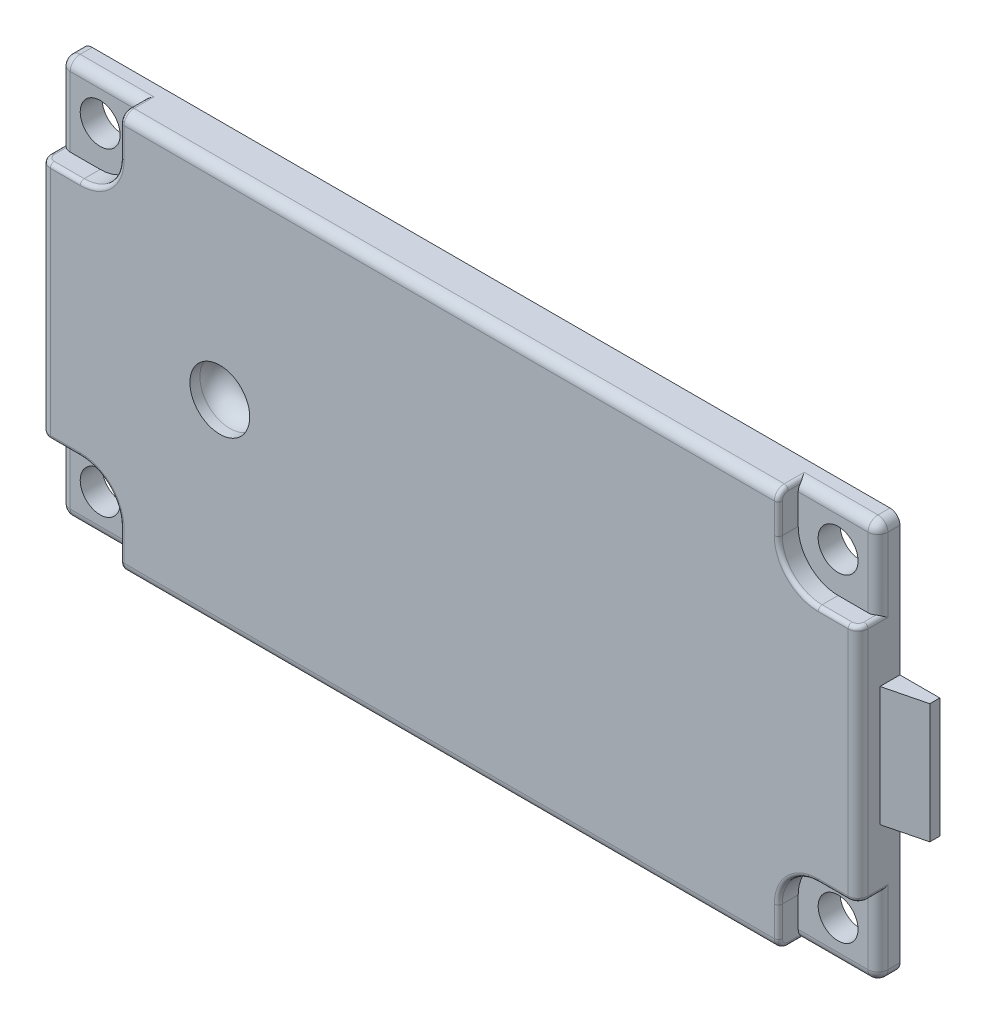
SolidWorks part; units mm, degrees
ref_plane "Front Plane" through (0, 0, 0) normal (0, 0, 1) x (1, 0, 0)
ref_plane "Top Plane" through (0, 0, 0) normal (0, 1, 0) x (1, 0, 0)
ref_plane "Right Plane" through (0, 0, 0) normal (1, 0, 0) x (0, 0, -1)
sketch "Sketch1" plane through (0, 0, 0) normal (0, 0, 1) x (1, 0, 0)
  line L0 (-20.5, -10) -> (20.5, 10) construction
  line L1 (-20.5, 10) -> (20.5, 10)
  line L2 (-20.5, 10) -> (-20.5, -10)
  line L3 (-20.5, -10) -> (20.5, -10)
  line L4 (20.5, 10) -> (20.5, -10)
  line L5 (-13.6353, 0) -> (-19.2524, 0) construction
  line L6 (0, 4.4253) -> (0, 7.9981) construction
  circle A0 centre (-18.5, 7.9981) radius 1
  circle A1 centre (-18.5, -7.9981) radius 1
  circle A2 centre (18.5, 7.9981) radius 1
  circle A3 centre (18.5, -7.9981) radius 1
  point P4 (0, 0)
  dimension "D3" = 2
  dimension "D1" = 20
  dimension "D2" = 41
  dimension "D4" = 2.0019
  dimension "D5" = 2
extrude "Extrude1" add sketch "Sketch1" along normal blind 2.1
sketch "Sketch2" plane through (0, 0, 2.1) normal (0, 0, 1) x (1, 0, 0)
  line L0 (0, 0) -> (31.1572, 0) construction
  line L1 (20.5, 10) -> (16.5, 10)
  line L2 (20.5, 10) -> (20.5, 6)
  line L3 (20.5, 6) -> (18.5, 6)
  line L4 (16.5, 10) -> (16.5, 8)
  line L5 (0, 0) -> (0, 18.9663) construction
  line L6 (16.5, -10) -> (16.5, -8)
  line L7 (20.5, -6) -> (18.5, -6)
  line L8 (20.5, -10) -> (20.5, -6)
  line L9 (20.5, -10) -> (16.5, -10)
  line L10 (-20.5, -10) -> (-16.5, -10)
  line L11 (-20.5, -10) -> (-20.5, -6)
  line L12 (-20.5, -6) -> (-18.5, -6)
  line L13 (-16.5, -10) -> (-16.5, -8)
  line L14 (-16.5, 10) -> (-16.5, 8)
  line L15 (-20.5, 6) -> (-18.5, 6)
  line L16 (-20.5, 10) -> (-20.5, 6)
  line L17 (-20.5, 10) -> (-16.5, 10)
  arc A0 (16.5, 8) -> (18.5, 6) centre (18.5, 8) ccw
  arc A3 (16.5, -8) -> (18.5, -6) centre (18.5, -8) cw
  arc A4 (-16.5, -8) -> (-18.5, -6) centre (-18.5, -8) ccw
  arc A7 (-16.5, 8) -> (-18.5, 6) centre (-18.5, 8) cw
  dimension "D3" = 2
  dimension "D1" = 4
  dimension "D2" = 4
extrude "Cut-Extrude1" cut sketch "Sketch2" against normal blind 1
fillet "Fillet1" radius 0.5 16 edges at (20.5, 0, 2.1) (-20.5, 0, 2.1) (0, -10, 2.1) (0, 10, 2.1) (-18.5, -10, 1.1) (-20.5, -8, 1.1) (-18.5, 10, 1.1) (-20.5, 8, 1.1) (18.5, 10, 1.1) (20.5, 8, 1.1) (20.5, -8, 1.1) (18.5, -10, 1.1) (-20.5, 10, 0.55) (-20.5, -10, 0.55) (20.5, 10, 0.55) (20.5, -10, 0.55)
fillet "Fillet2" radius 0.2 28 edges at (20.3536, -6, 1.9536) (19.25, -6, 2.1) (16.5, -9.8536, 1.9536) (16.5, -8.75, 2.1) (-16.5, -9.8536, 1.9536) (-16.5, -8.75, 2.1) (-20.3536, -6, 1.9536) (-19.25, -6, 2.1) (-20.3536, 6, 1.9536) (-19.25, 6, 2.1) (-16.5, 9.8536, 1.9536) (-16.5, 8.75, 2.1) (16.5, 9.8536, 1.9536) (16.5, 8.75, 2.1) (20.3536, 6, 1.9536) (19.25, 6, 2.1) (17.0858, -6.5858, 2.1) (-17.0858, -6.5858, 2.1) (-17.0858, 6.5858, 2.1) (17.0858, 6.5858, 2.1) (-16.5, -10, 1.1) (-20.5, -6, 1.1) (20.5, -6, 1.1) (16.5, -10, 1.1) (-20.5, 6, 1.1) (-16.5, 10, 1.1) (16.5, 10, 1.1) (20.5, 6, 1.1)
sketch "Sketch3" plane through (0, 0, 2.1) normal (0, 0, 1) x (1, 0, 0)
  line L0 (-20.5, -5.8) -> (-20.5, 5.8) construction
  line L1 (-16.3, 10) -> (16.3, 10) construction
  circle A0 centre (-11.5, 0) radius 1.5
  dimension "D1" = 3
  dimension "D2" = 9
  dimension "D3" = 10
extrude "Cut-Extrude2" cut sketch "Sketch3" against normal blind 1.5
fillet "Fillet3" radius 1 1 edges at (-10, 0, 0.6)
sketch "Sketch4" plane through (0, 0, 0) normal (0, 1, 0) x (1, 0, 0)
  line L0 (20.5, 0) -> (22.5, 0)
  line L1 (22.5, 0) -> (22.5, -0.5)
  line L2 (22.5, -0.5) -> (20.5, -1)
  line L3 (20.5, -1) -> (20.5, 0)
  dimension "D1" = 2
  dimension "D2" = 1
  dimension "D3" = 0.5
extrude "Extrude2" add sketch "Sketch4" along normal blind 3 and the other way blind 3
